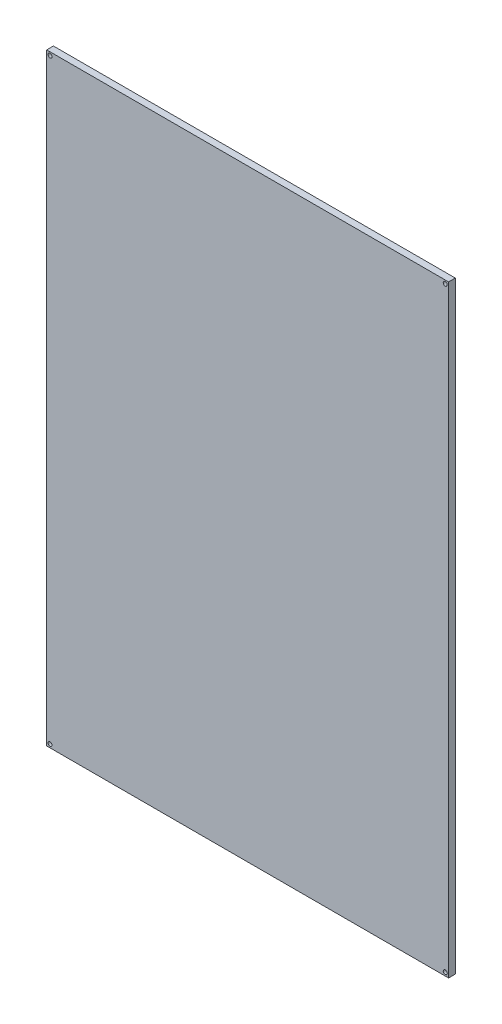
SolidWorks part; units mm, degrees
material "Oak"
ref_plane "Front Plane" through (0, 0, 0) normal (0, 0, 1) x (1, 0, 0)
ref_plane "Top Plane" through (0, 0, 0) normal (0, 1, 0) x (1, 0, 0)
ref_plane "Right Plane" through (0, 0, 0) normal (1, 0, 0) x (0, 0, -1)
sketch "Sketch1" plane through (0, 0, 0) normal (0, 0, 1) x (1, 0, 0)
  line L1 (-150, 225) -> (150, 225)
  line L2 (-150, 225) -> (-150, -225)
  line L3 (-150, -225) -> (150, -225)
  line L4 (150, 225) -> (150, -225)
  line L5 (-150, 225) -> (150, -225) construction
  line L6 (-150, -225) -> (150, 225) construction
  point P0 (0, 0)
  dimension "D1" = 450
  dimension "D2" = 300
extrude "Boss-Extrude1" add sketch "Sketch1" along normal blind 5
sketch "Sketch2" plane through (0, 0, 5) normal (0, 0, 1) x (1, 0, 0)
  line L0 (-150, 225) -> (-150, -225) construction
  line L1 (-150, -225) -> (150, -225) construction
  line L2 (150, -225) -> (150, 225) construction
  line L3 (150, 225) -> (-150, 225) construction
  circle A0 centre (-147.5, -222.5) radius 1.5
  circle A1 centre (-147.5, 222.5) radius 1.5
  circle A2 centre (147.5, -222.5) radius 1.5
  circle A3 centre (147.5, 222.5) radius 1.5
  point P8 (-143.0453, 218.1621)
  point P11 (147.4335, -222.5)
  point P14 (143.7421, 218.1621)
  point P21 (-130.3117, 221.5659)
  dimension "D3" = 3
  dimension "D6" = 3
  dimension "D9" = 3
  dimension "D12" = 3
  dimension "D1" = 2.5
  dimension "D2" = 2.5
  dimension "D4" = 2.5
  dimension "D5" = 2.5
  dimension "D7" = 2.5
  dimension "D8" = 2.5
  dimension "D10" = 2.5
  dimension "D11" = 2.5
extrude "Cut-Extrude1" cut sketch "Sketch2" against normal through all
